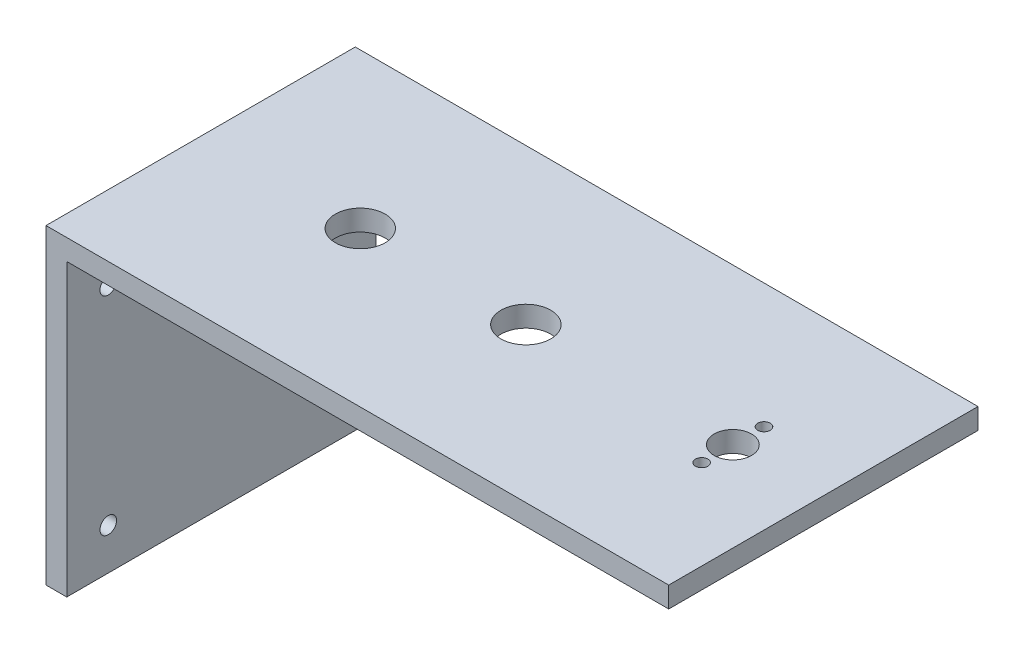
SolidWorks part; units mm, degrees
ref_plane "Front Plane" through (0, 0, 0) normal (0, 0, 1) x (1, 0, 0)
ref_plane "Top Plane" through (0, 0, 0) normal (0, 1, 0) x (1, 0, 0)
ref_plane "Right Plane" through (0, 0, 0) normal (1, 0, 0) x (0, 0, -1)
sketch "Croquis1" plane through (0, 0, 0) normal (0, 1, 0) x (1, 0, 0)
  line L1 (-75, -37.25) -> (75, -37.25)
  line L2 (-75, -37.25) -> (-75, 37.25)
  line L3 (-75, 37.25) -> (75, 37.25)
  line L4 (75, -37.25) -> (75, 37.25)
  point P4 (0, 37.25)
  point P6 (-75, 0)
  dimension "D1" = 74.5
  dimension "D2" = 150
extrude "Saliente-Extruir1" add sketch "Croquis1" along normal blind 5
sketch "Croquis2" plane through (0, 0, 0) normal (0, -1, 0) x (1, 0, 0)
  line L0 (-75, 37.25) -> (-70, 37.25)
  line L1 (-75, 37.25) -> (75, 37.25) construction
  line L2 (-70, 37.25) -> (-70, -37.25)
  line L3 (75, -37.25) -> (-75, -37.25) construction
  line L4 (-70, -37.25) -> (-75, -37.25)
  line L5 (-75, -37.25) -> (-75, 37.25)
  dimension "D1" = 5
extrude "Saliente-Extruir2" add sketch "Croquis2" along normal blind 70
sketch "Croquis3" plane through (-70, 0, 0) normal (1, 0, 0) x (0, 0, -1)
  line L0 (37.25, 0) -> (-37.25, 0) construction
  line L1 (-37.25, -70) -> (-37.25, 0) construction
  line L2 (37.25, -70) -> (37.25, 0) construction
  line L3 (-37.25, -35) -> (37.25, -35) construction
  circle A0 centre (-27.25, -10) radius 2
  circle A1 centre (27.25, -10) radius 2
  circle A2 centre (27.25, -60) radius 2
  circle A3 centre (-27.25, -60) radius 2
  dimension "D5" = 4
  dimension "D6" = 4
  dimension "D1" = 10
  dimension "D2" = 10
  dimension "D3" = 10
  dimension "D4" = 10
extrude "Cortar-Extruir1" cut sketch "Croquis3" against normal blind 70
sketch "Croquis4" plane through (0, 5, 0) normal (0, 1, 0) x (1, 0, 0)
  line L1 (75, 37.25) -> (-75, 37.25) construction
  line L2 (75, -37.25) -> (75, 37.25) construction
  line L3 (53.45, -0.25) -> (-36.55, 0) construction
  line L5 (53.45, -0.25) -> (53.45, 9.7679) construction
  circle A1 centre (-36.55, 0) radius 6
  circle A2 centre (53.45, -0.25) radius 4.5
  circle A3 centre (53.45, 7.25) radius 1.5
  circle A4 centre (53.4292, -7.75) radius 1.5
  circle A5 centre (3.4498, -0.1111) radius 6
  dimension "D3" = 9
  dimension "D4" = 12
  dimension "D5" = 3
  dimension "D11" = 3
  dimension "D13" = 7.5
  dimension "D14" = 12
  dimension "D2" = 37.5
  dimension "D6" = 36.55
  dimension "D7" = 7.5
  dimension "D8" = 21.55
  dimension "D9" = 7.5
  dimension "D10" = 10.0179
  dimension "D12" = 90
  dimension "D15" = 40
extrude "Cortar-Extruir2" cut sketch "Croquis4" against normal blind 70
